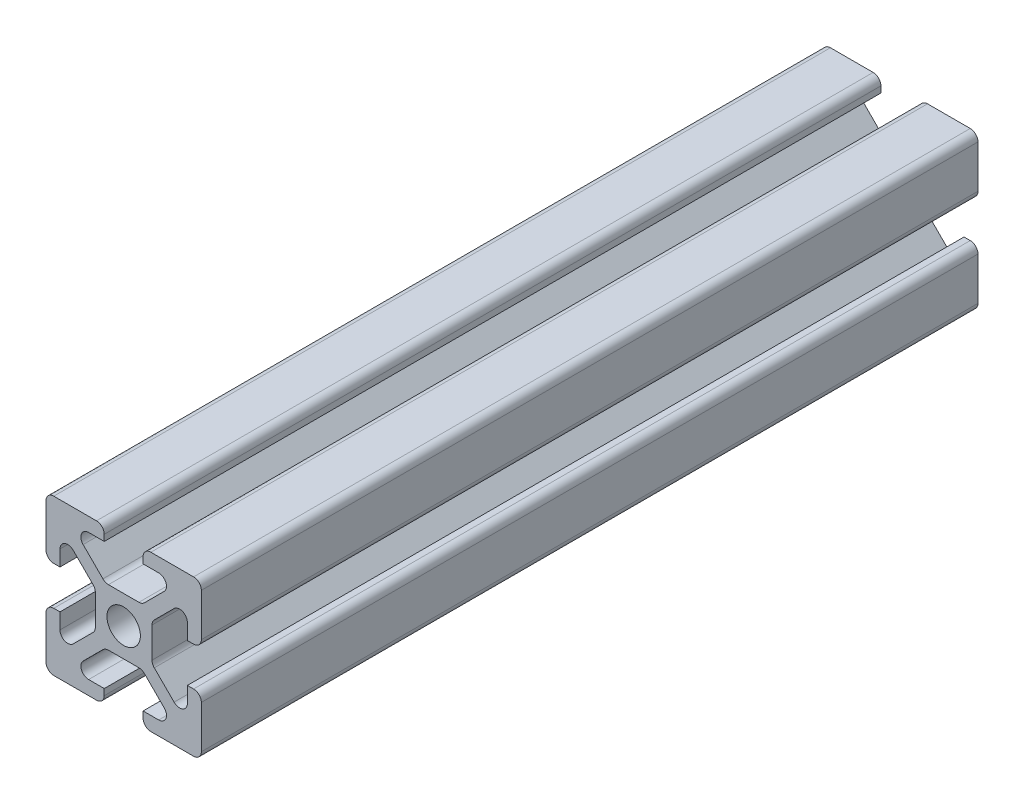
SolidWorks part; units mm, degrees
ref_plane "Piano frontale" through (0, 0, 0) normal (0, 0, 1) x (1, 0, 0)
ref_plane "Piano superiore" through (0, 0, 0) normal (0, 1, 0) x (1, 0, 0)
ref_plane "Piano destro" through (0, 0, 0) normal (1, 0, 0) x (0, 0, -1)
ref_plane "Piano1" through (0, 0, 0) normal (0, 0, -1) x (-1, 0, 0)
sketch "Schizzo1" plane through (0, 0, 0) normal (0, 0, -1) x (-1, 0, 0)
  line L0 (8.2, 2.5) -> (9, 2.5)
  line L1 (10, 3.5) -> (10, 9)
  line L2 (9, 10) -> (3.5, 10)
  line L3 (2.5, 9) -> (2.5, 8.2)
  line L4 (2.5, 8.2) -> (4.513, 8.2)
  line L5 (5.2201, 6.4929) -> (2.6701, 3.9429)
  line L6 (1.963, 3.65) -> (-1.963, 3.65)
  line L7 (-2.6701, 3.9429) -> (-5.2201, 6.4929)
  line L8 (-4.513, 8.2) -> (-2.5, 8.2)
  line L9 (-2.5, 8.2) -> (-2.5, 9)
  line L10 (-3.5, 10) -> (-9, 10)
  line L11 (-10, 9) -> (-10, 3.5)
  line L12 (-9, 2.5) -> (-8.2, 2.5)
  line L13 (-8.2, 2.5) -> (-8.2, 4.513)
  line L14 (-6.4929, 5.2201) -> (-3.9429, 2.6701)
  line L15 (-3.65, 1.963) -> (-3.65, -1.963)
  line L16 (-3.9429, -2.6701) -> (-6.4929, -5.2201)
  line L17 (-8.2, -4.513) -> (-8.2, -2.5)
  line L18 (-8.2, -2.5) -> (-9, -2.5)
  line L19 (-10, -3.5) -> (-10, -9)
  line L20 (-9, -10) -> (-3.5, -10)
  line L21 (-2.5, -9) -> (-2.5, -8.2)
  line L22 (-2.5, -8.2) -> (-4.513, -8.2)
  line L23 (-5.2201, -6.4929) -> (-2.6701, -3.9429)
  line L24 (-1.963, -3.65) -> (1.963, -3.65)
  line L25 (2.6701, -3.9429) -> (5.2201, -6.4929)
  line L26 (4.513, -8.2) -> (2.5, -8.2)
  line L27 (2.5, -8.2) -> (2.5, -9)
  line L28 (3.5, -10) -> (9, -10)
  line L29 (10, -9) -> (10, -3.5)
  line L30 (9, -2.5) -> (8.2, -2.5)
  line L31 (8.2, -2.5) -> (8.2, -4.513)
  line L32 (6.4929, -5.2201) -> (3.9429, -2.6701)
  line L33 (3.65, -1.963) -> (3.65, 1.963)
  line L34 (3.9429, 2.6701) -> (6.4929, 5.2201)
  line L35 (8.2, 4.513) -> (8.2, 2.5)
  circle A0 centre (0, 0) radius 2.15
  arc A1 (9, 2.5) -> (10, 3.5) centre (9, 3.5) ccw
  arc A2 (10, 9) -> (9, 10) centre (9, 9) ccw
  arc A3 (3.5, 10) -> (2.5, 9) centre (3.5, 9) ccw
  arc A4 (4.513, 8.2) -> (5.2201, 6.4929) centre (4.513, 7.2) cw
  arc A5 (2.6701, 3.9429) -> (1.963, 3.65) centre (1.963, 4.65) cw
  arc A6 (-1.963, 3.65) -> (-2.6701, 3.9429) centre (-1.963, 4.65) cw
  arc A7 (-5.2201, 6.4929) -> (-4.513, 8.2) centre (-4.513, 7.2) cw
  arc A8 (-2.5, 9) -> (-3.5, 10) centre (-3.5, 9) ccw
  arc A9 (-9, 10) -> (-10, 9) centre (-9, 9) ccw
  arc A10 (-10, 3.5) -> (-9, 2.5) centre (-9, 3.5) ccw
  arc A11 (-8.2, 4.513) -> (-6.4929, 5.2201) centre (-7.2, 4.513) cw
  arc A12 (-3.9429, 2.6701) -> (-3.65, 1.963) centre (-4.65, 1.963) cw
  arc A13 (-3.65, -1.963) -> (-3.9429, -2.6701) centre (-4.65, -1.963) cw
  arc A14 (-6.4929, -5.2201) -> (-8.2, -4.513) centre (-7.2, -4.513) cw
  arc A15 (-9, -2.5) -> (-10, -3.5) centre (-9, -3.5) ccw
  arc A16 (-10, -9) -> (-9, -10) centre (-9, -9) ccw
  arc A17 (-3.5, -10) -> (-2.5, -9) centre (-3.5, -9) ccw
  arc A18 (-4.513, -8.2) -> (-5.2201, -6.4929) centre (-4.513, -7.2) cw
  arc A19 (-2.6701, -3.9429) -> (-1.963, -3.65) centre (-1.963, -4.65) cw
  arc A20 (1.963, -3.65) -> (2.6701, -3.9429) centre (1.963, -4.65) cw
  arc A21 (5.2201, -6.4929) -> (4.513, -8.2) centre (4.513, -7.2) cw
  arc A22 (2.5, -9) -> (3.5, -10) centre (3.5, -9) ccw
  arc A23 (9, -10) -> (10, -9) centre (9, -9) ccw
  arc A24 (10, -3.5) -> (9, -2.5) centre (9, -3.5) ccw
  arc A25 (8.2, -4.513) -> (6.4929, -5.2201) centre (7.2, -4.513) cw
  arc A26 (3.9429, -2.6701) -> (3.65, -1.963) centre (4.65, -1.963) cw
  arc A27 (3.65, 1.963) -> (3.9429, 2.6701) centre (4.65, 1.963) cw
  arc A28 (6.4929, 5.2201) -> (8.2, 4.513) centre (7.2, 4.513) cw
  point P94 (0, 3.65)
  point P95 (3.65, 0)
extrude "Estrusione-Estrusione1" add sketch "Schizzo1" against normal blind 100
